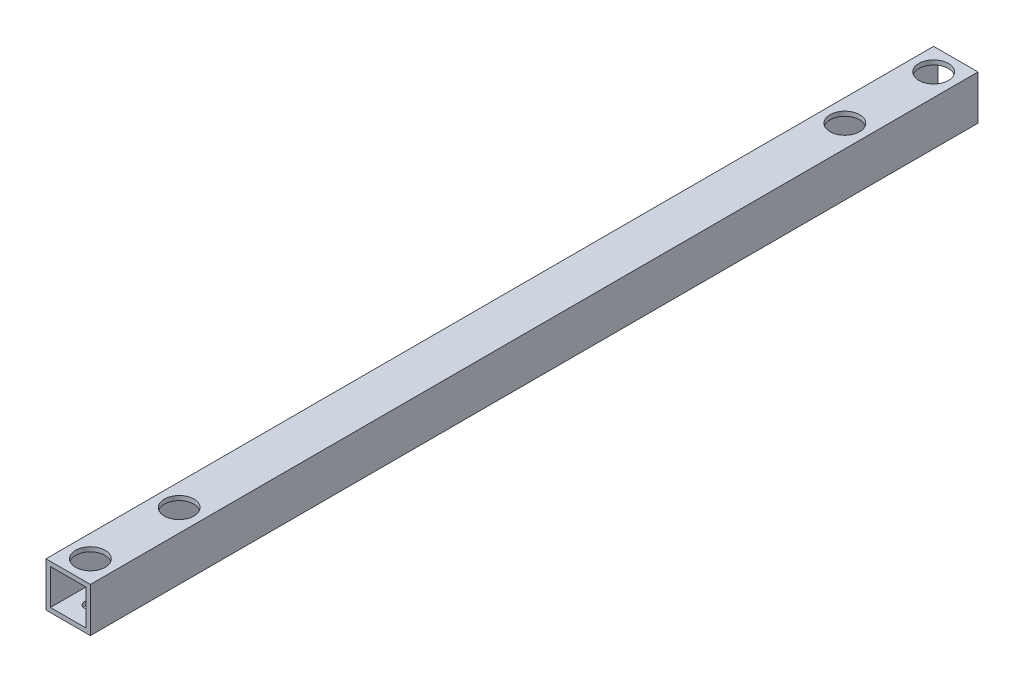
SolidWorks part; units mm, degrees
material "6063-T5"
ref_plane "正面" through (0, 0, 0) normal (0, 0, 1) x (1, 0, 0)
ref_plane "平面" through (0, 0, 0) normal (0, 1, 0) x (1, 0, 0)
ref_plane "右側面" through (0, 0, 0) normal (1, 0, 0) x (0, 0, -1)
sketch "ｽｹｯﾁ1" plane through (0, 0, 0) normal (0, 0, 1) x (1, 0, 0)
  line L1 (-7.5, -7.5) -> (7.5, -7.5)
  line L2 (-7.5, -7.5) -> (-7.5, 7.5)
  line L3 (-7.5, 7.5) -> (7.5, 7.5)
  line L4 (7.5, -7.5) -> (7.5, 7.5)
  line L5 (-7.5, -7.5) -> (7.5, 7.5) construction
  line L6 (-7.5, 7.5) -> (7.5, -7.5) construction
  line L7 (-6, -6) -> (6, -6)
  line L8 (-6, -6) -> (-6, 6)
  line L9 (-6, 6) -> (6, 6)
  line L10 (6, -6) -> (6, 6)
  line L11 (-6, -6) -> (6, 6) construction
  line L12 (-6, 6) -> (6, -6) construction
  point P0 (0, 0)
  point P6 (0, 0)
  dimension "D1" = 1.5
  dimension "D2" = 15
  dimension "D3" = 15
extrude "ﾎﾞｽ - 押し出し1" add sketch "ｽｹｯﾁ1" along normal blind 300
sketch "ｽｹｯﾁ5" plane through (0, -7.5, 0) normal (0, -1, 0) x (-1, 0, 0)
  line L0 (7.5, 0) -> (-7.5, 0) construction
  line L1 (7.5, -300) -> (7.5, 0) construction
  line L2 (7.5, -300) -> (-7.5, -300) construction
  circle A0 centre (0, -37.5) radius 2
  circle A1 centre (0, -7.5) radius 2
  circle A2 centre (0, -292.5) radius 2
  circle A3 centre (0, -262.5) radius 2
  dimension "D1" = 7.5
  dimension "D2" = 4
  dimension "D3" = 4
  dimension "D4" = 30
  dimension "D5" = 7.5
  dimension "D6" = 7.5
  dimension "D8" = 7.5
  dimension "D7" = 2
extrude "ｶｯﾄ - 押し出し4" cut sketch "ｽｹｯﾁ5" against normal blind 20
sketch "ｽｹｯﾁ8" plane through (0, 7.5, 0) normal (0, 1, 0) x (1, 0, 0)
  circle A0 centre (0, -292.5) radius 5
  circle A1 centre (0, -262.5) radius 5
  circle A2 centre (0, -37.5) radius 5
  circle A3 centre (0, -7.5) radius 5
  dimension "D1" = 10
  dimension "D2" = 10
  dimension "D3" = 10
  dimension "D4" = 10
extrude "ｶｯﾄ - 押し出し5" cut sketch "ｽｹｯﾁ8" against normal blind 10
